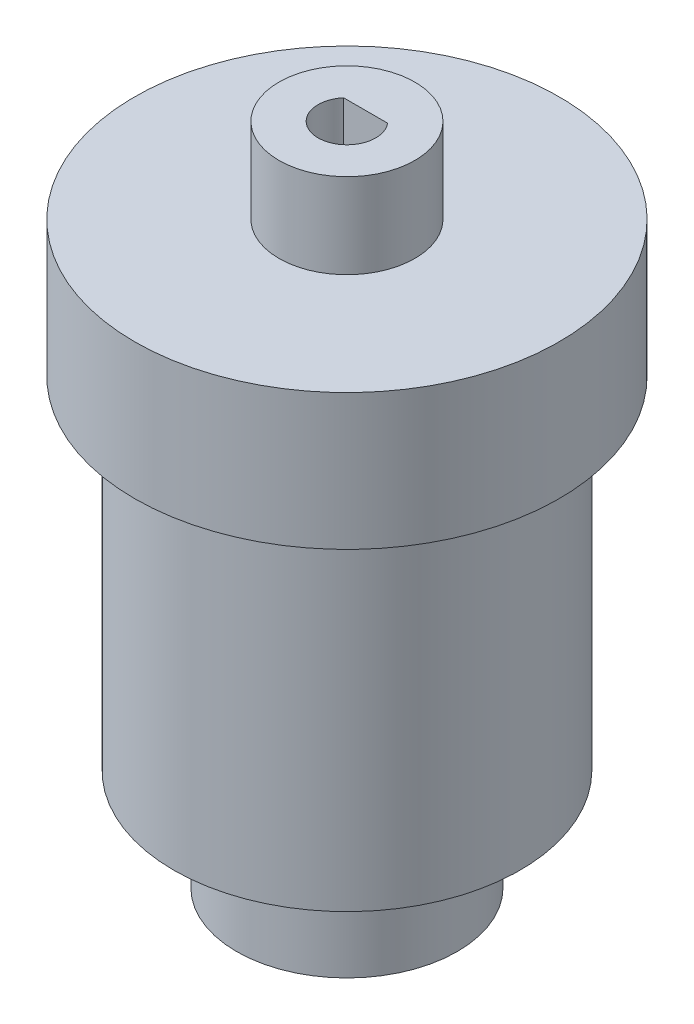
SolidWorks part; units mm, degrees
ref_plane "Front Plane" through (0, 0, 0) normal (0, 0, 1) x (1, 0, 0)
ref_plane "Top Plane" through (0, 0, 0) normal (0, 1, 0) x (1, 0, 0)
ref_plane "Right Plane" through (0, 0, 0) normal (1, 0, 0) x (0, 0, -1)
sketch "Sketch1" plane through (0, 0, 0) normal (0, 1, 0) x (1, 0, 0)
  circle A0 centre (0, 0) radius 10.2
  dimension "D1" = 20.4
extrude "Boss-Extrude1" add sketch "Sketch1" along normal blind 20.1
sketch "Sketch6" plane through (0, 20.1, 0) normal (0, 1, 0) x (1, 0, 0)
  line L0 (-3.6, 6.8631) -> (3.6, 6.8631)
  line L1 (-3.6, 6.8631) -> (-5.0359, 8.8702)
  line L2 (3.6, 6.8631) -> (5.0359, 8.8702)
  line L3 (-5.0359, 8.8702) -> (-4.8878, 10.936)
  line L4 (-4.8878, 10.936) -> (5.0359, 10.936)
  line L5 (5.0359, 10.936) -> (5.0359, 8.8702)
  circle A0 centre (0, 0) radius 7.75 construction
  circle A2 centre (0, 0) radius 10.2 construction
  dimension "D2" = 15.5
  dimension "D1" = 7.2
extrude "Cut-Extrude3" cut sketch "Sketch6" against normal through all
sketch "Sketch7" plane through (0, 20.1, 0) normal (0, 1, 0) x (1, 0, 0)
  line L0 (-1.2247, 1.25) -> (1.2247, 1.25)
  arc A2 (-1.2247, 1.25) -> (1.2247, 1.25) centre (0, 0) ccw
  point P5 (0, 1.25)
  dimension "D1" = 3.5
  dimension "D2" = 1.25
sketch "Sketch9" plane through (0, 20.1, 0) normal (0, 1, 0) x (1, 0, 0)
  circle A0 centre (0, 0) radius 12.5
  dimension "D1" = 25
extrude "Boss-Extrude3" add sketch "Sketch9" along normal blind 8
sketch "Sketch10" plane through (0, 28.1, 0) normal (0, 1, 0) x (1, 0, 0)
  circle A0 centre (0, 0) radius 4
  dimension "D1" = 8
extrude "Boss-Extrude4" add sketch "Sketch10" along normal blind 5
sketch "Sketch11" plane through (0, 33.1, 0) normal (0, 1, 0) x (1, 0, 0)
  line L0 (-1.2961, 1.1) -> (1.2961, 1.1)
  arc A0 (-1.2961, 1.1) -> (1.2961, 1.1) centre (0, 0) ccw
  point P5 (0, 1.1)
  dimension "D1" = 3.4
  dimension "D2" = 1.1
extrude "Cut-Extrude5" cut sketch "Sketch11" against normal blind 15
sketch "Sketch12" plane through (0, 0, 0) normal (0, -1, 0) x (1, 0, 0)
  circle A0 centre (0, 0) radius 6.5
  dimension "D1" = 13
extrude "Boss-Extrude5" add sketch "Sketch12" along normal blind 6
